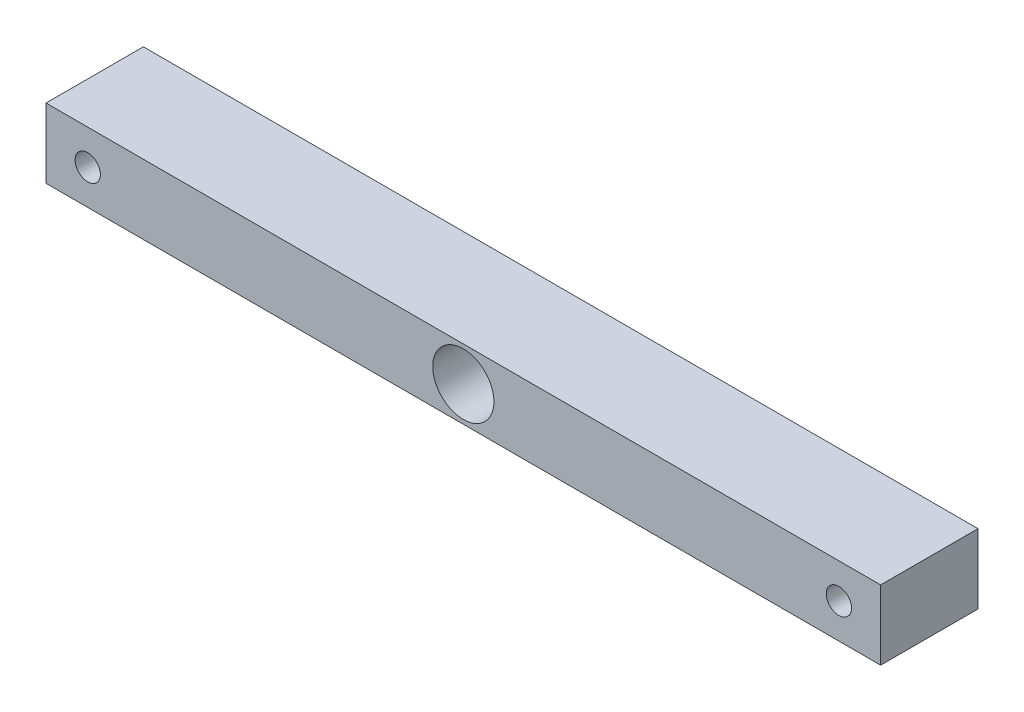
SolidWorks part; units mm, degrees
ref_plane "Front Plane" through (0, 0, 0) normal (0, 0, 1) x (1, 0, 0)
ref_plane "Top Plane" through (0, 0, 0) normal (0, 1, 0) x (1, 0, 0)
ref_plane "Right Plane" through (0, 0, 0) normal (1, 0, 0) x (0, 0, -1)
sketch "Sketch1" plane through (0, 0, 0) normal (0, 0, 1) x (1, 0, 0)
  line L1 (-150, -12.5) -> (150, -12.5)
  line L2 (-150, -12.5) -> (-150, 12.5)
  line L3 (-150, 12.5) -> (150, 12.5)
  line L4 (150, -12.5) -> (150, 12.5)
  line L5 (-150, -12.5) -> (150, 12.5) construction
  line L6 (-150, 12.5) -> (150, -12.5) construction
  point P0 (0, 0)
  dimension "D1" = 300
  dimension "D2" = 25
extrude "Boss-Extrude1" add sketch "Sketch1" along normal blind 35
sketch "Sketch2" plane through (0, 0, 35) normal (0, 0, 1) x (1, 0, 0)
  line L0 (-150, 0) -> (150, 0) construction
  line L1 (-150, 12.5) -> (-150, -12.5) construction
  line L2 (150, -12.5) -> (150, 12.5) construction
  circle A0 centre (-135, 0) radius 4.5424
  circle A1 centre (0, 0) radius 11
  circle A2 centre (135, 0) radius 4.5424
  dimension "D1" = 22
  dimension "D2" = 15
  dimension "D3" = 15
extrude "Cut-Extrude1" cut sketch "Sketch2" against normal through all
